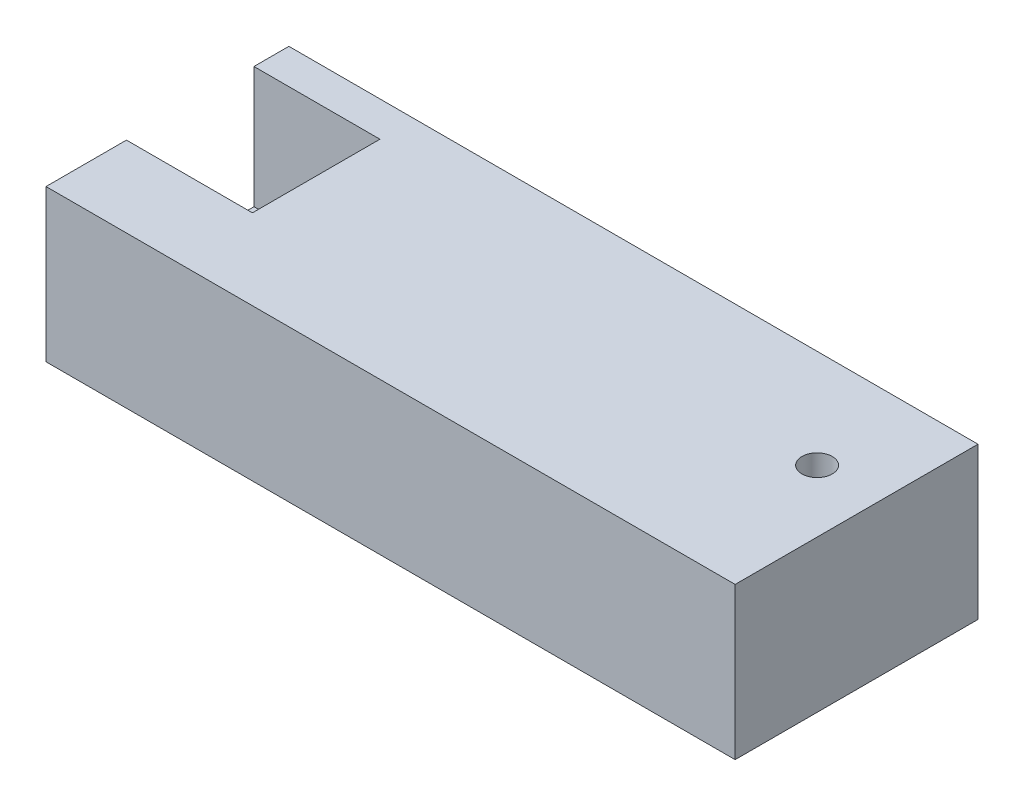
SolidWorks part; units mm, degrees
material "ABS"
ref_plane "Front Plane" through (0, 0, 0) normal (0, 0, 1) x (1, 0, 0)
ref_plane "Top Plane" through (0, 0, 0) normal (0, 1, 0) x (1, 0, 0)
ref_plane "Right Plane" through (0, 0, 0) normal (1, 0, 0) x (0, 0, -1)
sketch "Sketch1" plane through (0, 0, 0) normal (0, 1, 0) x (1, 0, 0)
  line L1 (-113.5, -40) -> (113.5, -40)
  line L2 (-113.5, -40) -> (-113.5, 40)
  line L3 (-113.5, 40) -> (113.5, 40)
  line L4 (113.5, -40) -> (113.5, 40)
  line L5 (-113.5, -40) -> (113.5, 40) construction
  line L6 (-113.5, 40) -> (113.5, -40) construction
  circle A0 centre (-93, 7.5) radius 5
  circle A1 centre (93, 7.5) radius 5
  point P0 (0, 0)
  dimension "D6" = 10
  dimension "D7" = 10
  dimension "D1" = 227
  dimension "D2" = 186
  dimension "D4" = 47.5
  dimension "D5" = 80
  dimension "D3" = 93
extrude "Boss-Extrude1" add sketch "Sketch1" along normal blind 50
sketch "Sketch2" plane through (0, 50, 0) normal (0, 1, 0) x (1, 0, 0)
  line L1 (-114, -13.5) -> (-72, -13.5)
  line L2 (-114, -13.5) -> (-114, 28.5)
  line L3 (-114, 28.5) -> (-72, 28.5)
  line L4 (-72, -13.5) -> (-72, 28.5)
  line L5 (-114, -13.5) -> (-72, 28.5) construction
  line L6 (-114, 28.5) -> (-72, -13.5) construction
  point P0 (-93, 7.5)
  dimension "D1" = 42
extrude "Cut-Extrude1" cut sketch "Sketch2" against normal blind 40
equation "\"D3@Sketch1\"=\"D2@Sketch1\"/2"
